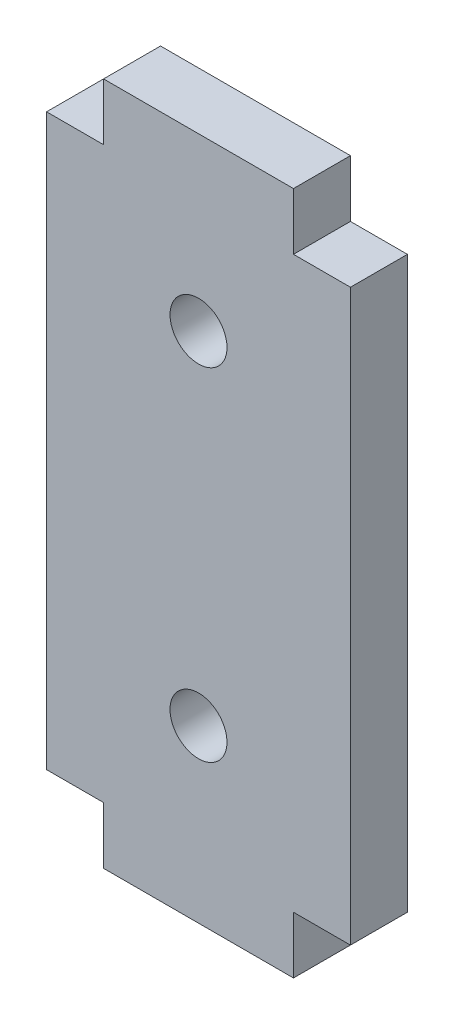
SolidWorks part; units mm, degrees
material "Acrylic (Medium-high impact)"
ref_plane "Front Plane" through (0, 0, 0) normal (0, 0, 1) x (1, 0, 0)
ref_plane "Top Plane" through (0, 0, 0) normal (0, 1, 0) x (1, 0, 0)
ref_plane "Right Plane" through (0, 0, 0) normal (1, 0, 0) x (0, 0, -1)
sketch "Sketch1" plane through (0, 0, 0) normal (0, 0, 1) x (1, 0, 0)
  line L0 (-11.2649, 0) -> (12.719, 0) construction
  line L1 (-5, 18) -> (5, 18)
  line L2 (-5, 18) -> (-5, 15)
  line L4 (5, 18) -> (5, 15)
  line L6 (-8, 15) -> (-5, 15)
  line L7 (-8, 15) -> (-8, -15)
  line L9 (8, 15) -> (8, -15)
  line L10 (5, 15) -> (8, 15)
  line L13 (5, -15) -> (8, -15)
  line L14 (-8, -15) -> (-5, -15)
  line L15 (5, -18) -> (5, -15)
  line L16 (-5, -18) -> (-5, -15)
  line L17 (-5, -18) -> (5, -18)
  circle A0 centre (0, 9) radius 1.5
  circle A2 centre (0, -9) radius 1.5
  point P6 (0, 18)
  point P15 (8, 0)
  point P19 (-8, 0)
  point P24 (5, 0)
  point P30 (-5, 0)
  dimension "D3" = 3
  dimension "D1" = 3
  dimension "D2" = 10
  dimension "D4" = 9
  dimension "D5" = 3
  dimension "D8" = 3
  dimension "D9" = 18
extrude "Boss-Extrude1" add sketch "Sketch1" along normal blind 3
